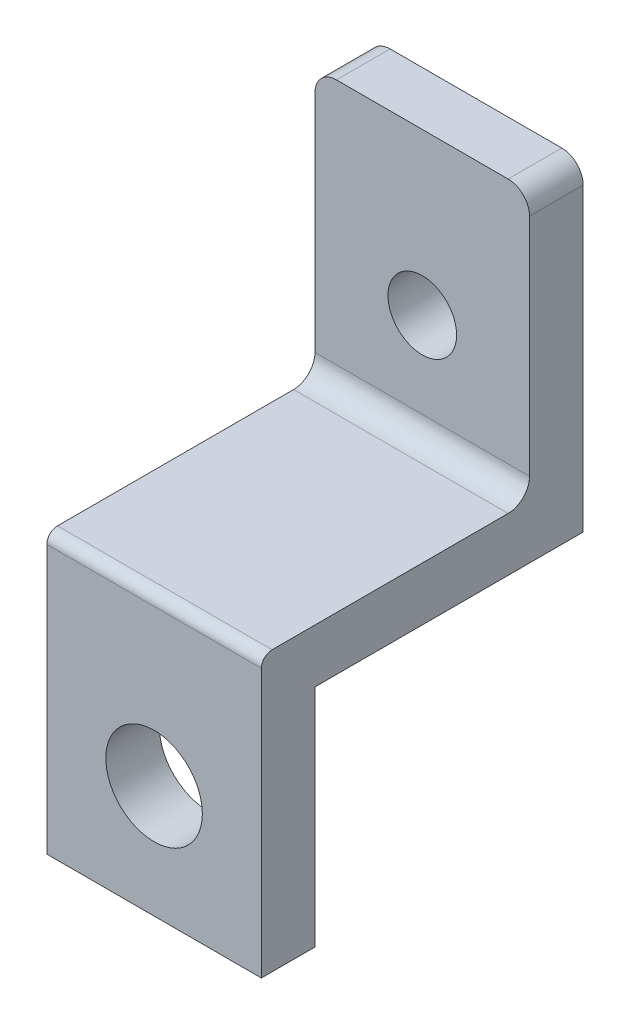
SolidWorks part; units mm, degrees
material "6061 Alloy"
ref_plane "前视基准面" through (0, 0, 0) normal (0, 0, 1) x (1, 0, 0)
ref_plane "上视基准面" through (0, 0, 0) normal (0, 1, 0) x (1, 0, 0)
ref_plane "右视基准面" through (0, 0, 0) normal (1, 0, 0) x (0, 0, -1)
other "Configuration Table"
sketch "Sketch1" plane through (0, 0, 0) normal (0, 0, 1) x (1, 0, 0)
  line L0 (0, 0) -> (0, 25) construction
  line L2 (-10, 10) -> (-10, -10)
  line L4 (10, 10) -> (10, -10)
  line L5 (-10, 10) -> (10, -10) construction
  line L6 (-10, -10) -> (10, 10) construction
  line L7 (0, 25) -> (0, 40) construction
  line L8 (0, 40) -> (0, 44) construction
  line L9 (10, 44) -> (-10, 44)
  line L10 (-10, 44) -> (-10, 10)
  line L11 (10, 44) -> (10, 10)
  line L12 (-10, -10) -> (-10, -11)
  line L13 (-10, -11) -> (10, -11)
  line L14 (10, -11) -> (10, -10)
  line L15 (0, 0) -> (0, -0.5) construction
  circle A0 centre (0, 0) radius 4.5 construction
  circle A1 centre (0, 25) radius 3 construction
  circle A2 centre (0, 40) radius 2.5 construction
  circle A3 centre (0, -0.5) radius 4.5
  dimension "D1" = 20
  dimension "D3" = 9
  dimension "D5" = 6
  dimension "D7" = 5
  dimension "D10" = 0.5
  dimension "D2" = 20
  dimension "D4" = 25
  dimension "D6" = 15
  dimension "D8" = 4
  dimension "D9" = 1
extrude "Boss-Extrude1" add sketch "Sketch1" along normal blind 5
sketch "Sketch2" plane through (0, 0, 0) normal (0, 0, -1) x (-1, 0, 0)
  line L1 (-10, -10) -> (10, -10) construction
  line L2 (-10, -10) -> (-10, 10) construction
  line L3 (-10, 10) -> (10, 10) construction
  line L4 (10, -10) -> (10, 10) construction
  line L5 (-10, -10) -> (10, 10) construction
  line L6 (-10, 10) -> (10, -10) construction
  line L7 (-10, 49) -> (10, 49)
  line L8 (-10, 49) -> (-10, 10)
  line L9 (-10, 10) -> (10, 10)
  line L10 (10, 49) -> (10, 10)
  point P0 (0, 0)
  dimension "D1" = 20
  dimension "D2" = 20
extrude "Boss-Extrude2" add sketch "Sketch2" along normal blind 25
sketch "Sketch3" plane through (10, 0, 0) normal (1, 0, 0) x (0, 0, -1)
  line L0 (0, 10) -> (0, 15) construction
  line L1 (0, 15) -> (-5, 15)
  line L2 (-5, -11) -> (-5, 44) construction
  line L7 (20, 15) -> (0, 15)
  line L8 (20, 15) -> (20, 49)
  line L9 (25, 49) -> (0, 49) construction
  line L10 (20, 49) -> (-5, 49)
  line L11 (-5, 49) -> (-5, 15)
  dimension "D1" = 5
extrude "Cut-Extrude1" cut sketch "Sketch3" against normal blind 30
mirror "Mirror1" [suppressed]
delete or keep bodies "Body-Delete/Keep 1" [suppressed] type delete bodies bodies 109
sketch "Sketch4" plane through (0, 0, -20) normal (0, 0, 1) x (1, 0, 0)
  line L0 (0, 49) -> (0, 40) construction
  line L1 (-10, 49) -> (10, 49) construction
  line L2 (0, 40) -> (0, 25) construction
  circle A0 centre (0, 40) radius 2.6 construction
  circle A1 centre (0, 25) radius 3.2
  dimension "D1" = 9
  dimension "D2" = 15
extrude "Cut-Extrude2" cut sketch "Sketch4" against normal blind 10
fillet "Fillet1" radius 2 1 edges at (0, 15, -20)
fillet "Fillet2" radius 1 1 edges at (0, 15, 5)
sketch "Sketch5" plane through (0, 0, -20) normal (0, 0, 1) x (1, 0, 0)
  line L0 (-10, 49) -> (-10, 40)
  line L1 (-10, 17) -> (-10, 49) construction
  line L2 (-10, 40) -> (10, 40)
  line L3 (10, 17) -> (10, 49) construction
  line L4 (-10, 49) -> (10, 49)
  line L6 (-10, 49) -> (10, 49) construction
  line L7 (10, 49) -> (10, 40)
  dimension "D1" = 9
extrude "Cut-Extrude3" cut sketch "Sketch5" against normal blind 10
fillet "Fillet3" radius 2 2 edges at (-10, 40, -22.5) (10, 40, -22.5)
